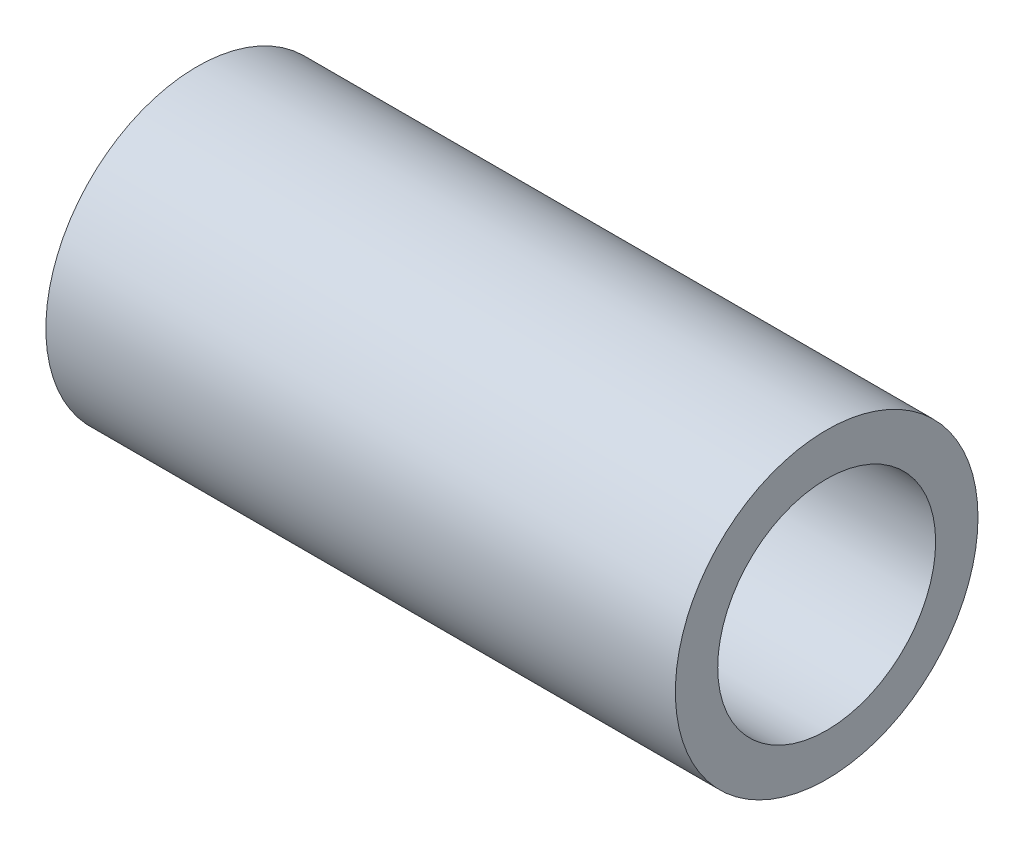
SolidWorks part; units mm, degrees
ref_plane "Piano frontale" through (0, 0, 0) normal (0, 0, 1) x (1, 0, 0)
ref_plane "Piano superiore" through (0, 0, 0) normal (0, 1, 0) x (1, 0, 0)
ref_plane "Piano destro" through (0, 0, 0) normal (1, 0, 0) x (0, 0, -1)
sketch "Schizzo1" plane through (0, 0, 0) normal (1, 0, 0) x (0, 0, -1)
  circle A0 centre (0, 0) radius 9
  dimension "D1" = 18
extrude "Estrusione-Sottile1" add sketch "Schizzo1" along normal mid plane 52 thin
